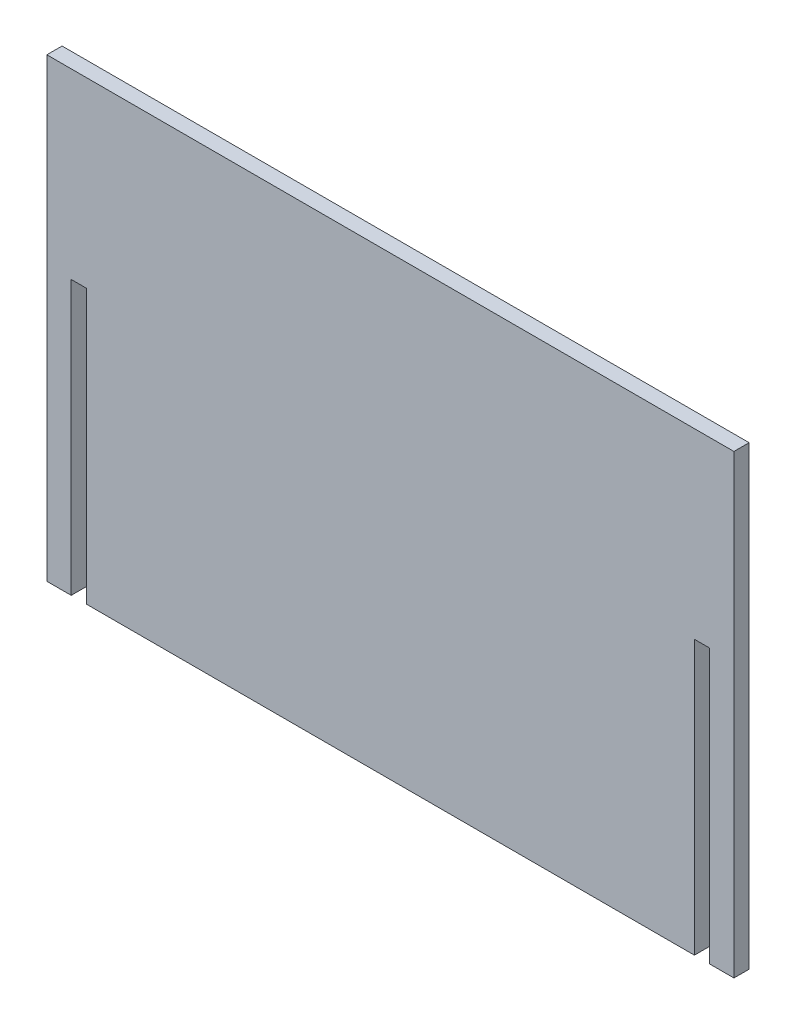
SolidWorks part; units mm, degrees
ref_plane "Plan de face" through (0, 0, 0) normal (0, 0, 1) x (1, 0, 0)
ref_plane "Plan de dessus" through (0, 0, 0) normal (0, 1, 0) x (1, 0, 0)
ref_plane "Plan de droite" through (0, 0, 0) normal (1, 0, 0) x (0, 0, -1)
sketch "Esquisse1" plane through (0, 0, 0) normal (0, 0, 1) x (1, 0, 0)
  line L0 (0, 0) -> (0, 150)
  line L1 (0, 150) -> (226, 150)
  line L2 (226, 150) -> (226, 0)
  line L3 (226, 0) -> (218, 0)
  line L4 (218, 0) -> (218, 90)
  line L5 (218, 90) -> (213, 90)
  line L6 (213, 90) -> (213, 0)
  line L7 (213, 0) -> (13, 0)
  line L8 (13, 0) -> (13, 90)
  line L9 (13, 90) -> (8, 90)
  line L10 (8, 90) -> (8, 0)
  line L11 (8, 0) -> (0, 0)
  dimension "D1" = 5
  dimension "D2" = 5
  dimension "D3" = 200
  dimension "D4" = 150
  dimension "D5" = 90
  dimension "D6" = 90
  dimension "D7" = 8
  dimension "D8" = 8
extrude "Boss.-Extru.1" add sketch "Esquisse1" along normal blind 5 contours L0 L1 L2 L3 L4 L5 L6 L7 L8 L9 L10 L11
